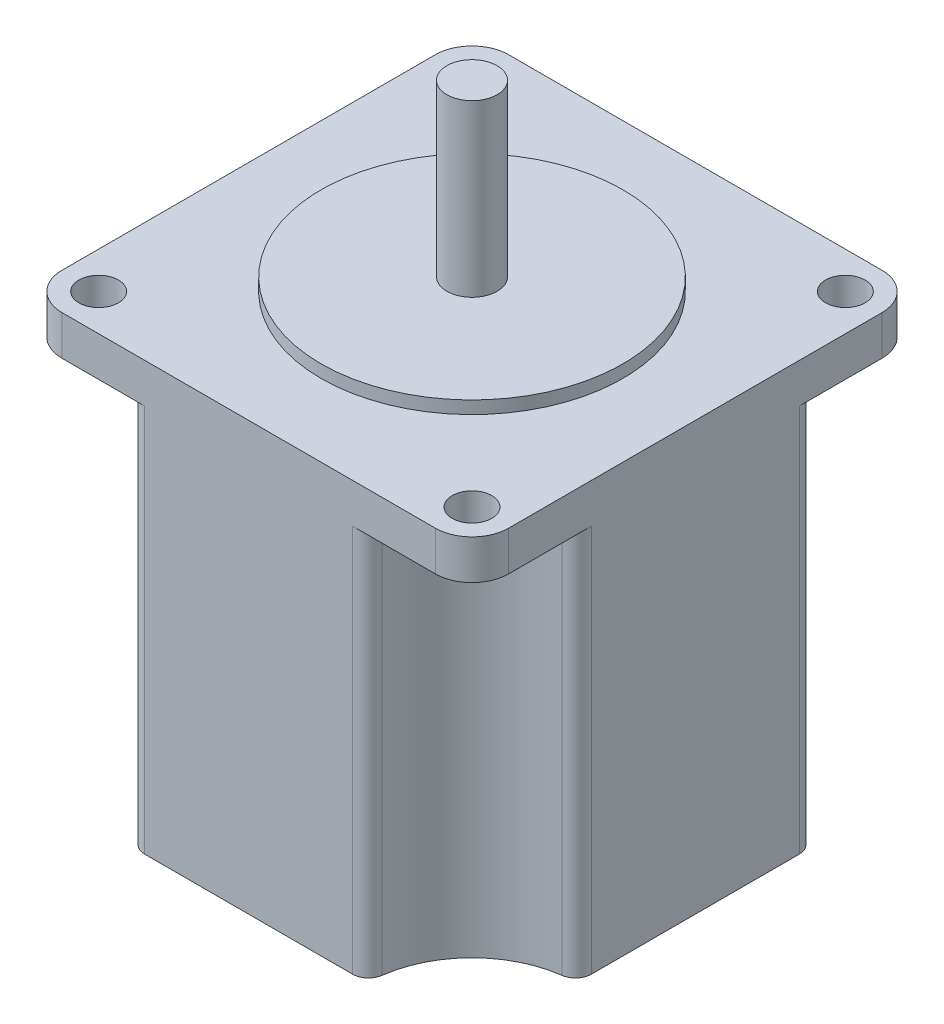
SolidWorks part; units mm, degrees
ref_plane "Front Plane" through (0, 0, 0) normal (0, 0, 1) x (1, 0, 0)
ref_plane "Top Plane" through (0, 0, 0) normal (0, 1, 0) x (1, 0, 0)
ref_plane "Right Plane" through (0, 0, 0) normal (1, 0, 0) x (0, 0, -1)
sketch "Sketch1" plane through (0, 0, 0) normal (0, 1, 0) x (1, 0, 0)
  line L0 (28.2, 56.4) -> (28.2, 0) construction
  line L1 (0, 0) -> (56.4, 0) construction
  line L2 (0, 0) -> (0, 56.4) construction
  line L3 (0, 56.4) -> (56.4, 56.4) construction
  line L4 (56.4, 0) -> (56.4, 56.4) construction
  line L5 (0, 28.2) -> (56.4, 28.2) construction
  line L6 (0, 51.77) -> (0, 4.63)
  line L7 (4.63, 56.4) -> (51.77, 56.4)
  line L8 (56.4, 51.77) -> (56.4, 4.63)
  line L9 (4.63, 0) -> (51.77, 0)
  circle A0 centre (4.63, 51.77) radius 2.5 construction
  arc A1 (4.63, 56.4) -> (0, 51.77) centre (4.63, 51.77) ccw
  arc A2 (51.77, 56.4) -> (56.4, 51.77) centre (51.77, 51.77) cw
  arc A3 (51.77, 0) -> (56.4, 4.63) centre (51.77, 4.63) ccw
  arc A4 (4.63, 0) -> (0, 4.63) centre (4.63, 4.63) cw
  dimension "D5" = 5
  dimension "D1" = 56.4
  dimension "D2" = 56.4
  dimension "D3" = 23.57
  dimension "D4" = 23.57
extrude "Boss-Extrude1" add sketch "Sketch1" along normal blind 54
sketch "Sketch2" plane through (0, 54, 0) normal (0, 1, 0) x (1, 0, 0)
  line L0 (0, 28.2) -> (56.4, 28.2) construction
  line L1 (0, 51.77) -> (0, 4.63) construction
  line L2 (56.4, 4.63) -> (56.4, 51.77) construction
  line L3 (28.2, 56.4) -> (28.2, 0) construction
  line L4 (51.77, 56.4) -> (4.63, 56.4) construction
  line L5 (4.63, 0) -> (51.77, 0) construction
  circle A0 centre (4.63, 51.77) radius 2.5
  arc A1 (4.63, 56.4) -> (0, 51.77) centre (4.63, 51.77) ccw construction
  circle A2 centre (51.77, 51.77) radius 2.5
  circle A3 centre (51.77, 4.63) radius 2.5
  circle A4 centre (4.63, 4.63) radius 2.5
  dimension "D1" = 5
extrude "Cut-Extrude1" cut sketch "Sketch2" against normal blind 54
sketch "Sketch3" plane through (0, 0, 0) normal (0, -1, 0) x (1, 0, 0)
  line L0 (15.0678, -56.4) -> (41.3322, -56.4)
  line L1 (0, -51.77) -> (0, -4.63) construction
  line L2 (4.63, 0) -> (51.77, 0) construction
  line L3 (0, -28.2) -> (56.4, -28.2) construction
  line L4 (56.4, -4.63) -> (56.4, -51.77) construction
  line L5 (28.2, 0) -> (28.2, -56.4) construction
  line L6 (51.77, -56.4) -> (4.63, -56.4) construction
  line L7 (0, -15.0678) -> (0, -41.3322)
  line L8 (15.0678, 0) -> (41.3322, 0)
  line L9 (56.4, -15.0678) -> (56.4, -41.3322)
  arc A0 (1.7368, -13.0852) -> (13.0852, -1.7368) centre (0, 0) ccw
  arc A1 (1.7368, -13.0852) -> (0, -15.0678) centre (2, -15.0678) ccw
  arc A2 (15.0678, 0) -> (13.0852, -1.7368) centre (15.0678, -2) ccw
  arc A3 (15.0678, -56.4) -> (13.0852, -54.6632) centre (15.0678, -54.4) cw
  arc A4 (1.7368, -43.3148) -> (0, -41.3322) centre (2, -41.3322) cw
  arc A5 (1.7368, -43.3148) -> (13.0852, -54.6632) centre (0, -56.4) cw
  arc A6 (41.3322, 0) -> (43.3148, -1.7368) centre (41.3322, -2) cw
  arc A7 (41.3322, -56.4) -> (43.3148, -54.6632) centre (41.3322, -54.4) ccw
  arc A8 (54.6632, -43.3148) -> (43.3148, -54.6632) centre (56.4, -56.4) ccw
  arc A9 (54.6632, -43.3148) -> (56.4, -41.3322) centre (54.4, -41.3322) ccw
  arc A10 (54.6632, -13.0852) -> (56.4, -15.0678) centre (54.4, -15.0678) cw
  arc A11 (54.6632, -13.0852) -> (43.3148, -1.7368) centre (56.4, 0) cw
  point P17 (0, -13.2)
  point P20 (13.2, 0)
  dimension "D3" = 2
  dimension "D1" = 15
  dimension "D2" = 15
extrude "Cut-Extrude3" cut sketch "Sketch3" against normal blind 49 flip side to cut
sketch "Sketch4" plane through (0, 54, 0) normal (0, 1, 0) x (1, 0, 0)
  line L0 (28.2, 0) -> (28.2, 56.4) construction
  line L1 (4.63, 0) -> (51.77, 0) construction
  line L2 (51.77, 56.4) -> (4.63, 56.4) construction
  circle A0 centre (28.2, 28.2) radius 19.05
  dimension "D1" = 38.1
extrude "Boss-Extrude2" add sketch "Sketch4" along normal blind 1.6
sketch "Sketch5" plane through (0, 55.6, 0) normal (0, 1, 0) x (1, 0, 0)
  line L0 (28.2, 9.15) -> (28.2, 47.25) construction
  circle A0 centre (28.2, 28.2) radius 3.175
  circle A3 centre (28.2, 28.2) radius 19.05 construction
  dimension "D1" = 6.35
extrude "Boss-Extrude3" add sketch "Sketch5" along normal blind 21.5
